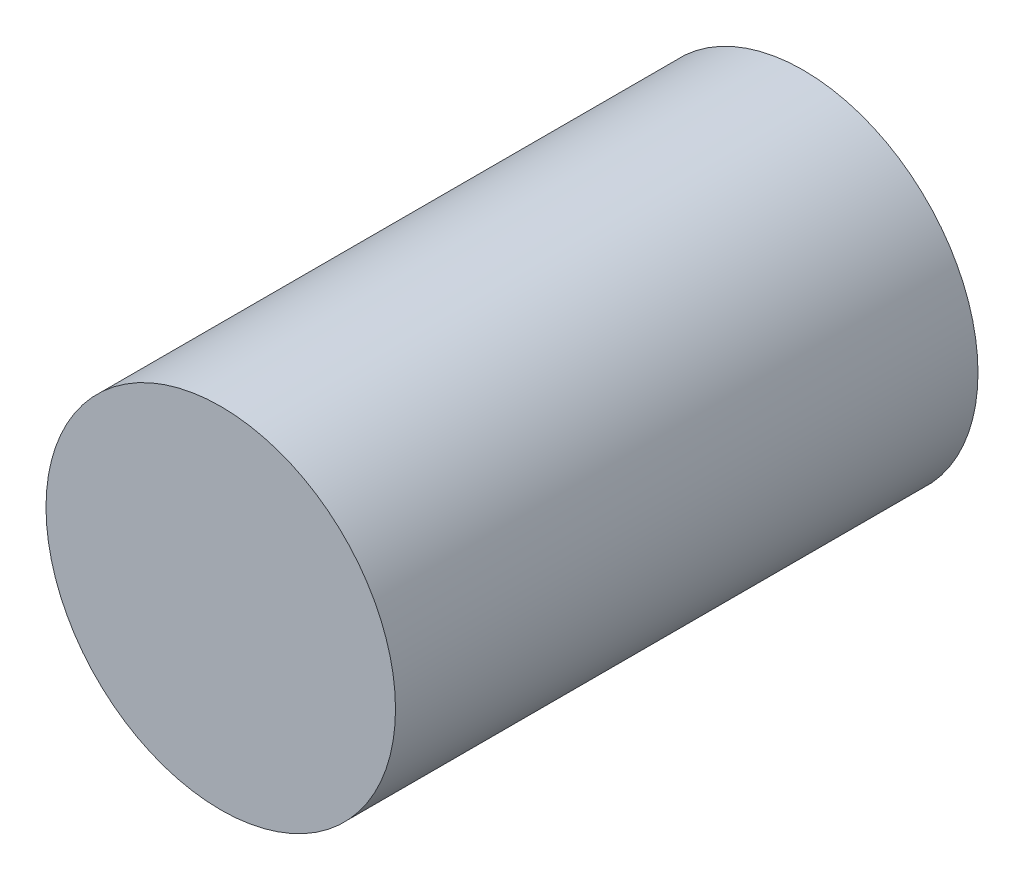
SolidWorks part; units mm, degrees
ref_plane "Plan de face" through (0, 0, 0) normal (0, 0, 1) x (1, 0, 0)
ref_plane "Plan de dessus" through (0, 0, 0) normal (0, 1, 0) x (1, 0, 0)
ref_plane "Plan de droite" through (0, 0, 0) normal (1, 0, 0) x (0, 0, -1)
sketch "Esquisse1" plane through (0, 0, 0) normal (0, 0, 1) x (1, 0, 0)
  circle A0 centre (0, 0) radius 15
extrude "Boss.-Extru.1" add sketch "Esquisse1" along normal blind 50
